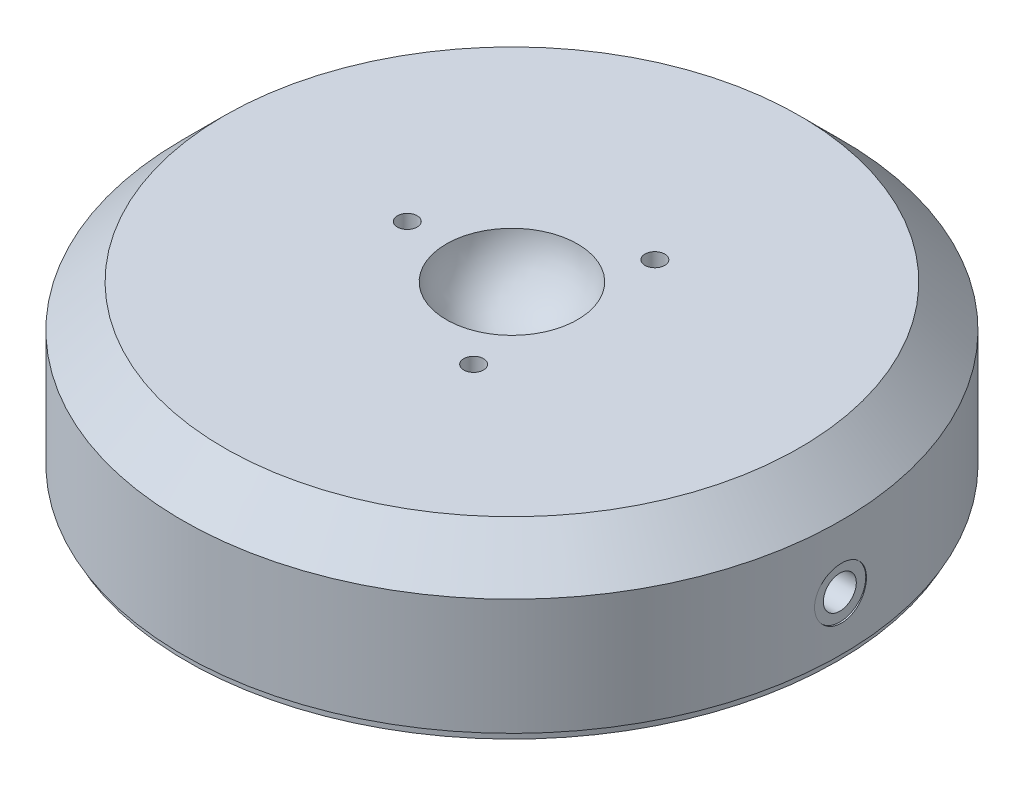
SolidWorks part; units mm, degrees
material "6061 Alloy"
ref_plane "Front Plane" through (0, 0, 0) normal (0, 0, 1) x (1, 0, 0)
ref_plane "Top Plane" through (0, 0, 0) normal (0, 1, 0) x (1, 0, 0)
ref_plane "Right Plane" through (0, 0, 0) normal (1, 0, 0) x (0, 0, -1)
sketch "Sketch1" plane through (0, 0, 0) normal (0, 0, 1) x (1, 0, 0)
  line L0 (0, 0) -> (49.9999, 0)
  line L1 (49.9999, 0) -> (49.9999, 17.6276)
  line L2 (49.9999, 17.6276) -> (43.6499, 23.9776)
  line L3 (43.6499, 23.9776) -> (9.9559, 23.9776)
  line L4 (0, 23.9776) -> (0, 0) construction
  line L5 (0, 14.5796) -> (1.1938, 14.5796)
  line L6 (1.1938, 14.5796) -> (1.1938, 15.0575)
  line L7 (0, 14.5796) -> (0, 0)
  arc A0 (1.1938, 15.0575) -> (9.9559, 23.9776) centre (0, 24.9936) ccw
  dimension "D1" = 10.0076
  dimension "D2" = 9.398
  dimension "D3" = 2.3876
  dimension "D4" = 1.016
  dimension "D5" = 23.9776
  dimension "D6" = 49.9999
  dimension "D7" = 6.35
  dimension "D8" = 45
revolve "Revolve1" add sketch "Sketch1" angle 360 about L4
sketch "Sketch2" plane through (0, 0, 0) normal (0, -1, 0) x (1, 0, 0)
  circle A0 centre (0, 0) radius 49.3395
  dimension "D1" = 98.679
hole_wizard "M5x0.8 Tapped Hole1" positions "3DSketch1" profile "Sketch4" tap size "M5x0.8" standard "Ansi Metric"
sketch3d "3DSketch1"
  point P0 (49.9999, 8.0772, 0)
  dimension "D1" = 15.9004
sketch "Sketch4" plane through (49.9999, 8.0772, 0) normal (0, 1, 0) x (0, 0, -1)
  line L0 (0, 0) -> (0, 48.2518)
  line L1 (0, 48.2518) -> (2.1, 46.99)
  line L2 (2.1, 46.99) -> (2.1, 7.62)
  line L3 (2.1, 7.62) -> (2.5, 7.62)
  line L4 (2.5, 7.62) -> (2.5, 0)
  line L5 (2.5, 0) -> (0, 0)
  line L10 (0, 48.2518) -> (-2.1, 46.99) construction
  line L11 (0, -6.35) -> (0, 107.95) construction
  dimension "Tap Drill Dia." = 4.2
  dimension "Tap Drill Depth" = 46.99
  dimension "Thread Major Dia." = 5
  dimension "Thread Depth" = 7.62
  dimension "Drill Angle" = 118
hole_wizard "M3x0.5 Tapped Hole1" positions "Sketch6" profile "Sketch5" tap size "M3x0.5" standard "Ansi Metric"
sketch "Sketch6" plane through (0, 23.9776, 0) normal (0, 1, 0) x (-1, 0, 0)
  line L0 (13.1877, 0) -> (-13.1877, 0) construction
  point P0 (15.875, 0)
  dimension "D1" = 15.875
sketch "Sketch5" plane through (-15.875, 23.9776, 0) normal (1, 0, 0) x (0, 0, 1)
  line L0 (0, 0) -> (0, 10.4031)
  line L1 (0, 10.4031) -> (1.25, 9.652)
  line L2 (1.25, 9.652) -> (1.25, 5.9944)
  line L3 (1.25, 5.9944) -> (1.5, 5.9944)
  line L4 (1.5, 5.9944) -> (1.5, 0)
  line L5 (1.5, 0) -> (0, 0)
  line L10 (0, 10.4031) -> (-1.25, 9.652) construction
  line L11 (0, -6.35) -> (0, 107.95) construction
  dimension "Tap Drill Dia." = 2.5
  dimension "Tap Drill Depth" = 9.652
  dimension "Thread Major Dia." = 3
  dimension "Thread Depth" = 5.9944
  dimension "Drill Angle" = 118
pattern_circular "CirPattern1" count 3 every 120 about axis through (0, 0, 0) along (0, 1, 0) of "M3x0.5 Tapped Hole1"
hole_wizard "CBORE for #00 Binding Head Machine Screw1" positions "3DSketch2" profile "Sketch7" counterbore size "#00" standard "Ansi Inch"
sketch3d "3DSketch2"
  line L0 (42.3799, 8.0772, 0) -> (49.9374, 8.0772, 0) construction
  point P0 (49.9999, 8.0772, 0)
  point P1 (49.9999, 8.0772, 0)
  point P3 (49.9999, 8.0772, 0)
sketch "Sketch7" plane through (49.9999, 8.0772, 0) normal (0, 1, 0) x (0, 0, -1)
  line L0 (0, 0) -> (0, 6.7697)
  line L1 (0, 6.7697) -> (0.6985, 6.35)
  line L2 (0.6985, 6.35) -> (0.6985, 0.254)
  line L3 (0.6985, 0.254) -> (3.937, 0.254)
  line L4 (3.937, 0.254) -> (3.937, 0)
  line L5 (3.937, 0) -> (0, 0)
  line L10 (0, 6.7697) -> (-0.6985, 6.35) construction
  line L11 (0, -6.35) -> (0, 107.95) construction
  dimension "Hole Dia." = 1.397
  dimension "Hole Depth" = 6.35
  dimension "C'Bore Dia." = 7.874
  dimension "C'Bore Depth" = 0.254
  dimension "Drill Angle" = 118
extrude "Extrude1" add sketch "Sketch2" along normal blind 1.2192
